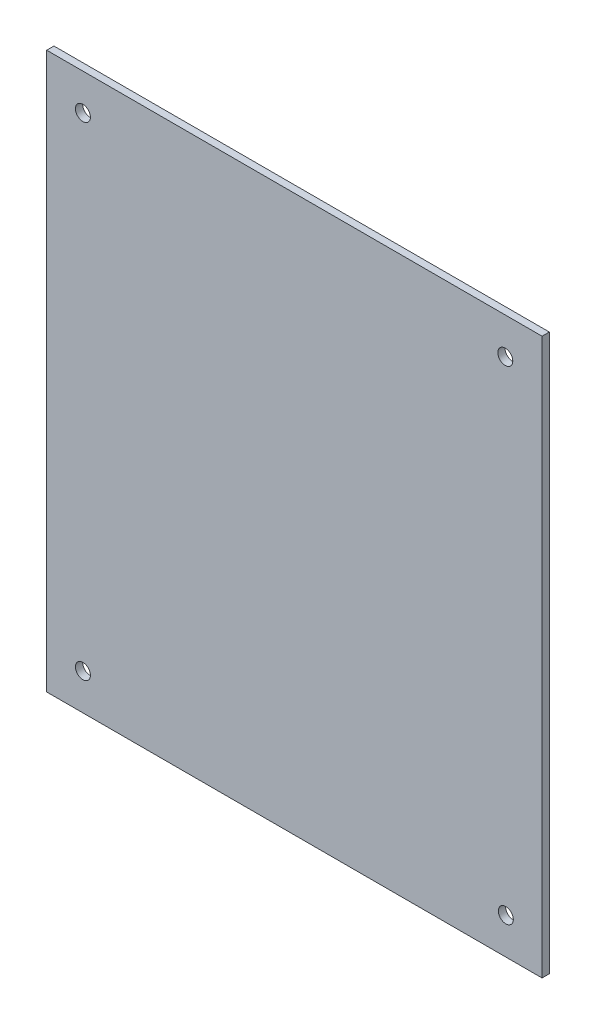
SolidWorks part; units mm, degrees
ref_plane "Alzado" through (0, 0, 0) normal (0, 0, 1) x (1, 0, 0)
ref_plane "Planta" through (0, 0, 0) normal (0, 1, 0) x (1, 0, 0)
ref_plane "Vista lateral" through (0, 0, 0) normal (1, 0, 0) x (0, 0, -1)
sketch "Croquis1" plane through (0, 0, 0) normal (0, 0, 1) x (1, 0, 0)
  line L0 (-87.5, 167.0051) -> (-87.5, -49832.9949) construction
  line L1 (-102.5, 115) -> (102.5, 115)
  line L2 (-102.5, 115) -> (-102.5, -115)
  line L3 (-102.5, -115) -> (102.5, -115)
  line L4 (102.5, 115) -> (102.5, -115)
  line L5 (-102.5, 115) -> (102.5, -115) construction
  line L6 (-102.5, -115) -> (102.5, 115) construction
  line L7 (-208.0544, 100) -> (49791.9456, 100) construction
  line L8 (-261.0645, -100) -> (49738.9355, -100) construction
  line L9 (87.5, 178.733) -> (87.5, -49821.267) construction
  circle A0 centre (-87.5, 100) radius 3.1
  circle A1 centre (87.2752, 100) radius 3.1
  circle A2 centre (-87.5, -100) radius 3.1
  circle A3 centre (87.5, -100) radius 3.1
  point P0 (0, 0)
  dimension "D7" = 6.2
  dimension "D1" = 205
  dimension "D2" = 230
  dimension "D3" = 15
  dimension "D4" = 15
  dimension "D5" = 15
  dimension "D6" = 15
extrude "Saliente-Extruir1" add sketch "Croquis1" along normal blind 3
